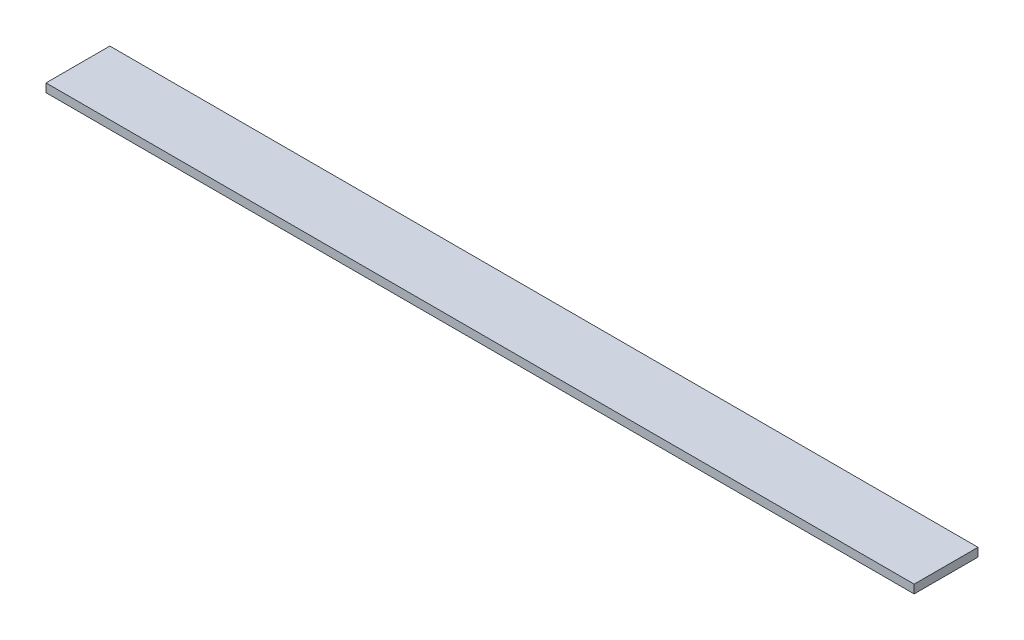
SolidWorks part; units mm, degrees
ref_plane "Спереди" through (0, 0, 0) normal (0, 0, 1) x (1, 0, 0)
ref_plane "Сверху" through (0, 0, 0) normal (0, 1, 0) x (1, 0, 0)
ref_plane "Справа" through (0, 0, 0) normal (1, 0, 0) x (0, 0, -1)
sketch "Эскиз1" plane through (0, 0, 0) normal (1, 0, 0) x (0, 0, -1)
  line L1 (-15, -2) -> (15, -2)
  line L2 (-15, -2) -> (-15, 2)
  line L3 (-15, 2) -> (15, 2)
  line L4 (15, -2) -> (15, 2)
  line L5 (-15, -2) -> (15, 2) construction
  line L6 (-15, 2) -> (15, -2) construction
  point P0 (0, 0)
  dimension "D1" = 4
  dimension "D2" = 30
extrude "Бобышка-Вытянуть1" add sketch "Эскиз1" along normal blind 408
